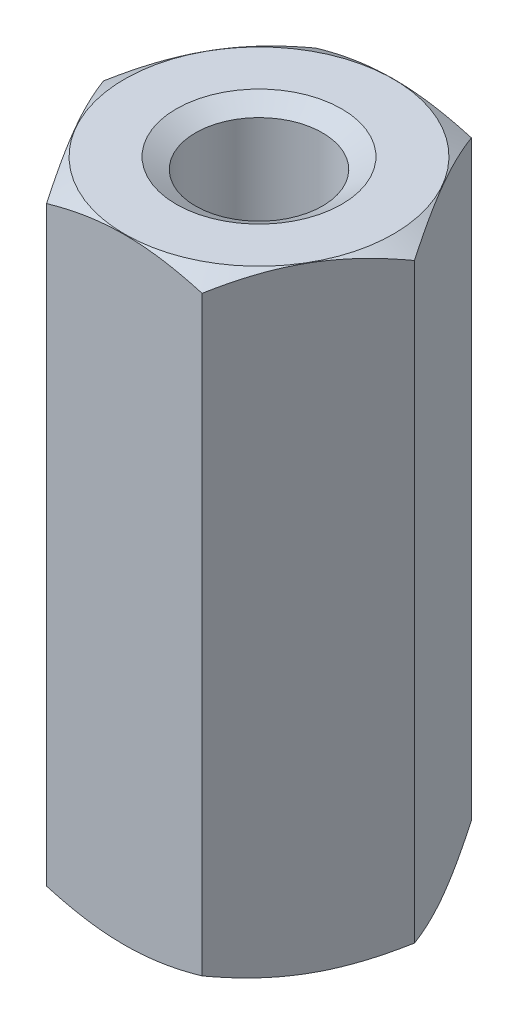
SolidWorks part; units mm, degrees
material "Stainless Steel (ferritic)"
ref_plane "Front Plane" through (0, 0, 0) normal (0, 0, 1) x (1, 0, 0)
ref_plane "Top Plane" through (0, 0, 0) normal (0, 1, 0) x (1, 0, 0)
ref_plane "Right Plane" through (0, 0, 0) normal (1, 0, 0) x (0, 0, -1)
sketch "Sketch1" plane through (0, 0, 0) normal (0, 1, 0) x (1, 0, 0)
  line L1 (4.0415, 0) -> (2.0207, 3.5) construction
  line L2 (2.0207, 3.5) -> (-2.0207, 3.5) construction
  line L3 (-2.0207, 3.5) -> (-4.0415, 0) construction
  line L4 (-4.0415, 0) -> (-2.0207, -3.5) construction
  line L5 (-2.0207, -3.5) -> (2.0207, -3.5) construction
  line L6 (2.0207, -3.5) -> (4.0415, 0) construction
  circle A0 centre (0, 0) radius 3.5 construction
  circle A1 centre (0, 0) radius 1.65
  circle A2 centre (0, 0) radius 4.0415
  dimension "D2" = 3.3
  dimension "D1" = 7
extrude "Boss-Extrude1" add sketch "Sketch1" along normal blind 16
cosmetic thread "Cosmetic Thread1" parameters "D2"=4
chamfer "Chamfer1" distance 0.55 angle 30 1 edges at (0, 16, 4.0415)
chamfer "Chamfer2" distance 0.55 angle 30 1 edges at (0, 0, 4.0415)
sketch "Sketch2" plane through (0, 0, 0) normal (0, -1, 0) x (1, 0, 0)
  line L0 (4.0415, 0) -> (2.0207, -3.5) construction
  line L1 (2.0207, -3.5) -> (-2.0207, -3.5) construction
  line L2 (-2.0207, -3.5) -> (-4.0415, 0) construction
  line L3 (-4.0415, 0) -> (-2.0207, 3.5) construction
  line L4 (-2.0207, 3.5) -> (2.0207, 3.5) construction
  line L5 (2.0207, 3.5) -> (4.0415, 0) construction
  line L6 (4.0415, 0) -> (2.0207, -3.5)
  line L7 (2.0207, -3.5) -> (-2.0207, -3.5)
  line L8 (-2.0207, -3.5) -> (-4.0415, 0)
  line L9 (-4.0415, 0) -> (-2.0207, 3.5)
  line L10 (-2.0207, 3.5) -> (2.0207, 3.5)
  line L11 (2.0207, 3.5) -> (4.0415, 0)
extrude "Cut-Extrude1" cut sketch "Sketch2" against normal through all flip side to cut
chamfer "Chamfer3" distance 0.5 angle 30 2 edges at (0, 0, 1.65) (0, 16, 1.65)
